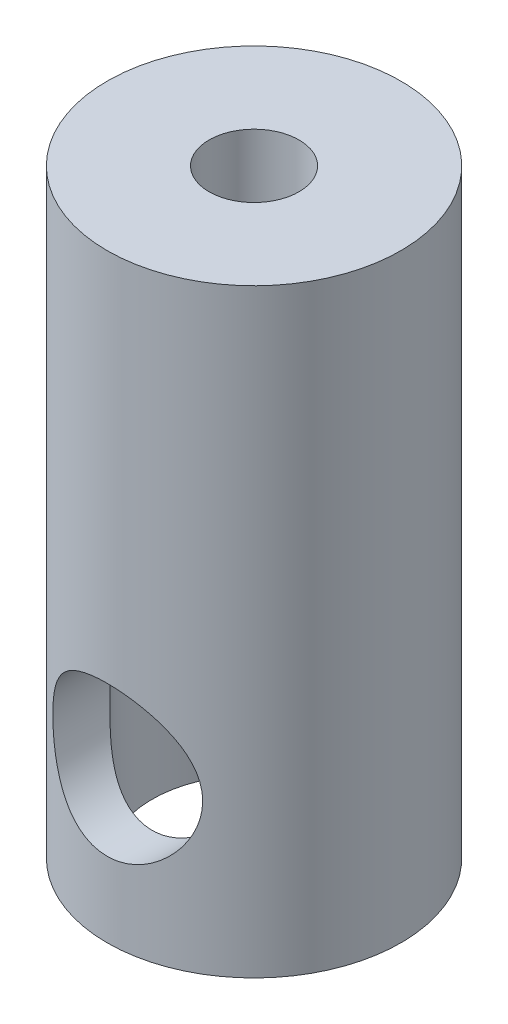
SolidWorks part; units mm, degrees
ref_plane "Front" through (0, 0, 0) normal (0, 0, 1) x (1, 0, 0)
ref_plane "Top" through (0, 0, 0) normal (0, 1, 0) x (1, 0, 0)
ref_plane "Right" through (0, 0, 0) normal (1, 0, 0) x (0, 0, -1)
sketch "Sketch1" plane through (0, 0, 0) normal (0, 1, 0) x (1, 0, 0)
  circle A0 centre (0, 0) radius 4.9
  dimension "D1" = 9.8
extrude "Boss-Extrude1" add sketch "Sketch1" along normal blind 20
sketch "Sketch2" plane through (0, 20, 0) normal (0, 1, 0) x (1, 0, 0)
  circle A0 centre (0, 0) radius 1.5
  dimension "D1" = 3
extrude "Cut-Extrude1" cut sketch "Sketch2" against normal blind 5
sketch "Sketch3" plane through (0, 0, 0) normal (0, -1, 0) x (1, 0, 0)
  circle A0 centre (0, 0) radius 3.4
  circle A1 centre (0, 0) radius 4.9 construction
  dimension "D1" = 1.5
extrude "Cut-Extrude2" cut sketch "Sketch3" against normal blind 10
sketch "Sketch4" plane through (0, 0, 0) normal (0, 0, 1) x (1, 0, 0)
  circle A0 centre (0, 5) radius 2.5
  dimension "D1" = 5
  dimension "D2" = 5
extrude "Cut-Extrude3" cut sketch "Sketch4" against normal through all both and the other way through all
